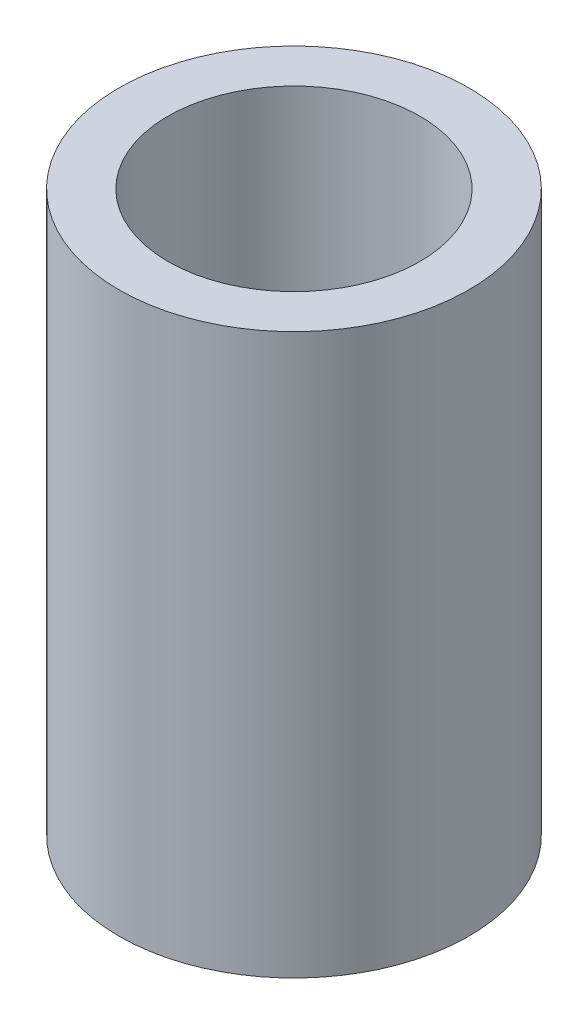
SolidWorks part; units mm, degrees
ref_plane "Front Plane" through (0, 0, 0) normal (0, 0, 1) x (1, 0, 0)
ref_plane "Top Plane" through (0, 0, 0) normal (0, 1, 0) x (1, 0, 0)
ref_plane "Right Plane" through (0, 0, 0) normal (1, 0, 0) x (0, 0, -1)
sketch "Sketch1" plane through (0, 0, 0) normal (0, 1, 0) x (1, 0, 0)
  circle A0 centre (-9.8653, -1.7403) radius 2.5
  circle A1 centre (-9.8653, -1.7403) radius 1.8
extrude "Boss-Extrude1" add sketch "Sketch1" along normal blind 8
